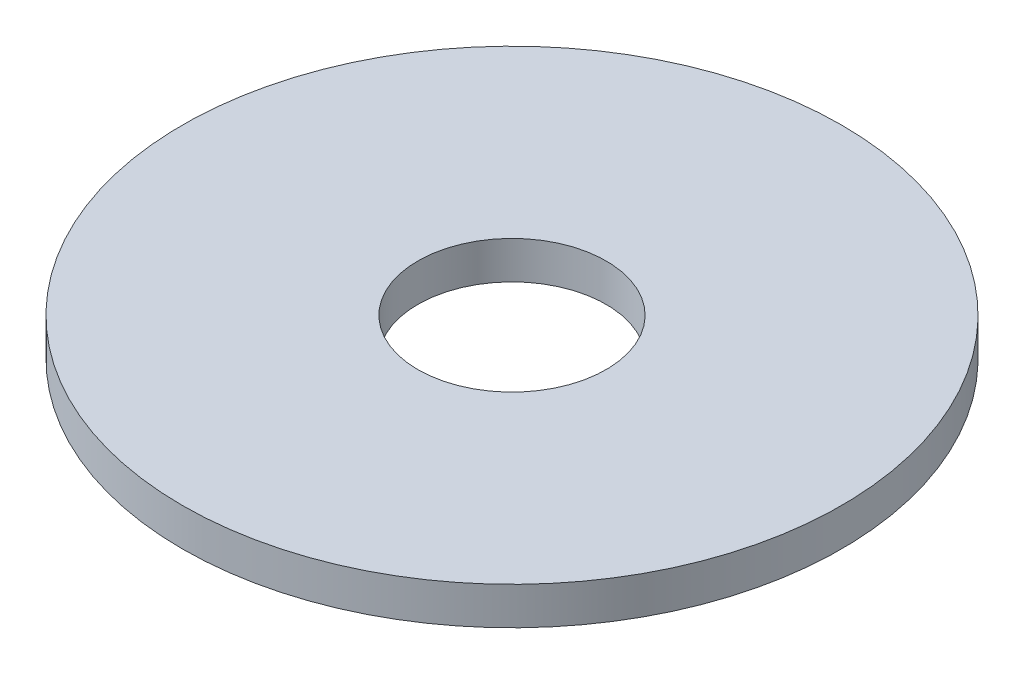
SolidWorks part; units mm, degrees
ref_plane "Front Plane" through (0, 0, 0) normal (0, 0, 1) x (1, 0, 0)
ref_plane "Top Plane" through (0, 0, 0) normal (0, 1, 0) x (1, 0, 0)
ref_plane "Right Plane" through (0, 0, 0) normal (1, 0, 0) x (0, 0, -1)
sketch "Sketch1" plane through (0, 0, 0) normal (0, 1, 0) x (1, 0, 0)
  circle A0 centre (0, 0) radius 35
  dimension "D1" = 70
extrude "Boss-Extrude1" add sketch "Sketch1" along normal blind 4
sketch "Sketch2" plane through (0, 4, 0) normal (0, 1, 0) x (1, 0, 0)
  circle A0 centre (0, 0) radius 10
  dimension "D1" = 20
extrude "Cut-Extrude1" cut sketch "Sketch2" against normal blind 10
